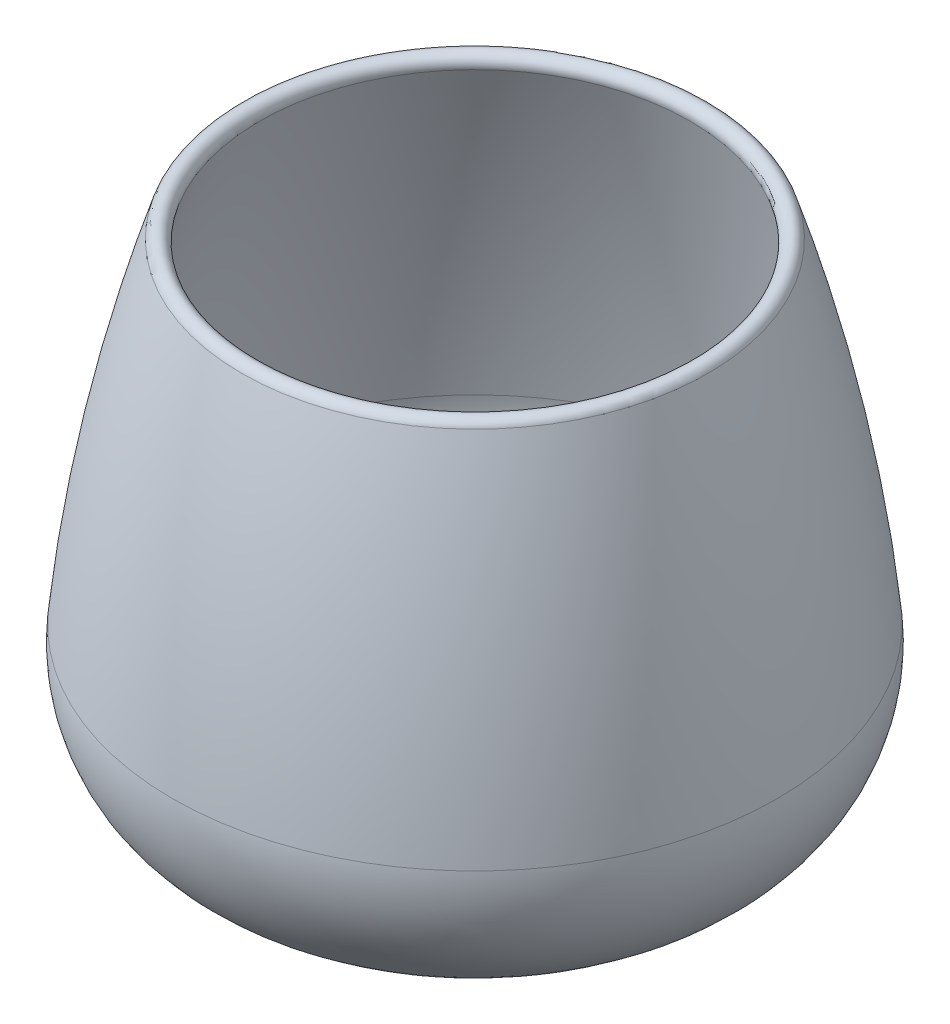
SolidWorks part; units mm, degrees
ref_plane "Front Plane" through (0, 0, 0) normal (0, 0, 1) x (1, 0, 0)
ref_plane "Top Plane" through (0, 0, 0) normal (0, 1, 0) x (1, 0, 0)
ref_plane "Right Plane" through (0, 0, 0) normal (1, 0, 0) x (0, 0, -1)
sketch "Sketch1" plane through (0, 0, 0) normal (0, 0, 1) x (1, 0, 0)
  line L0 (0, 0) -> (0, 95.564) construction
  line L1 (0, 0) -> (12.7, 0)
  line L2 (0, 68.58) -> (31.75, 68.58) construction
  line L3 (24.6239, 1.0854) -> (0, 1.0854) construction
  line L4 (41.1718, 23.1168) -> (0, 23.1168) construction
  line L5 (0, 2.54) -> (12.7, 2.54)
  line L6 (0, 2.54) -> (0, 0)
  line L7 (41.275, 21.0714) -> (41.275, 97.3158) construction
  arc A0 (12.7, 0) -> (24.6239, 1.0854) centre (12.7, 66.04) ccw
  arc A1 (24.6239, 1.0854) -> (41.1718, 23.1168) centre (20.955, 21.0714) ccw
  arc A2 (31.75, 68.58) -> (41.1718, 23.1168) centre (-182.3409, 0.5039) cw
  arc A3 (29.3294, 67.8103) -> (38.6447, 22.8611) centre (-182.3409, 0.5039) cw
  arc A4 (24.1653, 3.5836) -> (38.6447, 22.8611) centre (20.955, 21.0714) ccw
  arc A5 (12.7, 2.54) -> (24.1653, 3.5836) centre (12.7, 66.04) ccw
  arc A6 (29.3294, 67.8103) -> (31.75, 68.58) centre (30.5397, 68.1952) cw
  dimension "D4" = 66.04
  dimension "D6" = 20.32
  dimension "D1" = 31.75
  dimension "D2" = 12.7
  dimension "D3" = 68.58
  dimension "D5" = 22.8611
  dimension "D9" = 41.275
  dimension "D8" = 2.54
revolve "Revolve1" add sketch "Sketch1" angle 360 about L0
